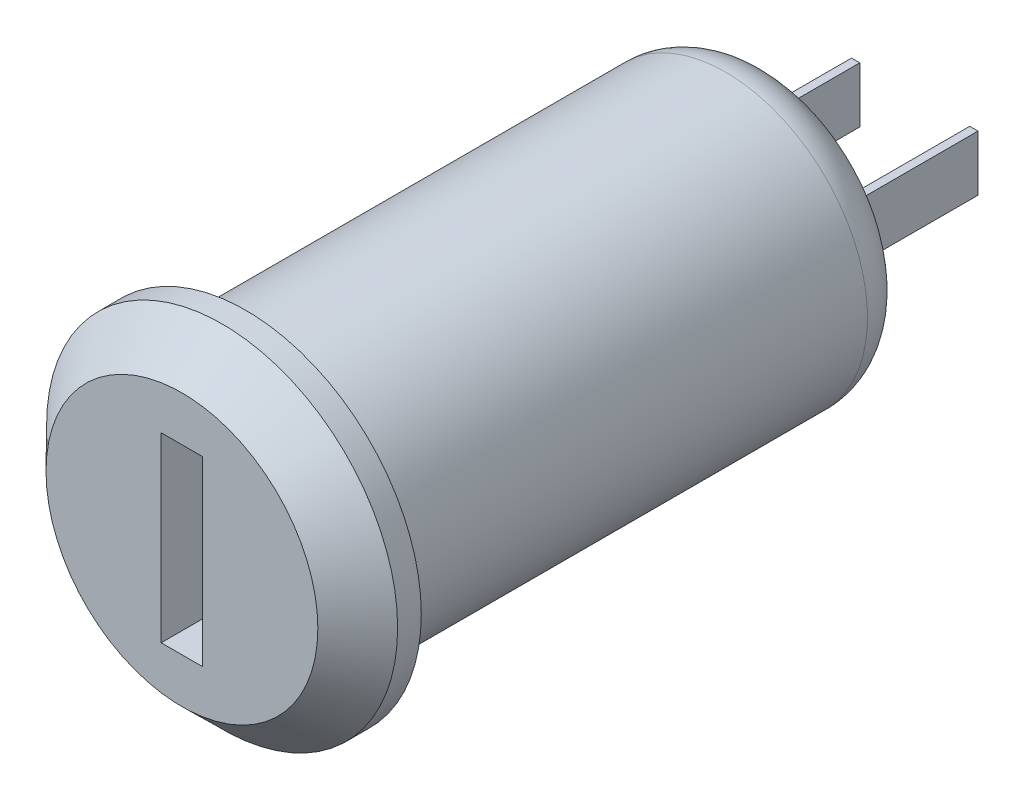
SolidWorks part; units mm, degrees
ref_plane "Front Plane" through (0, 0, 0) normal (0, 0, 1) x (1, 0, 0)
ref_plane "Top Plane" through (0, 0, 0) normal (0, 1, 0) x (1, 0, 0)
ref_plane "Right Plane" through (0, 0, 0) normal (1, 0, 0) x (0, 0, -1)
sketch "Sketch1" plane through (0, 0, 0) normal (0, 1, 0) x (1, 0, 0)
  line L0 (-7.425, -2.2335) -> (-5.75, -3.9335)
  line L2 (0, 0) -> (0, 21.0665)
  line L3 (0, 21.0665) -> (-6, 21.0665)
  line L4 (-6, -1.2335) -> (-6, 21.0665)
  line L5 (-6, -1.2335) -> (-7.425, -1.2335)
  line L6 (0, 0) -> (0, -3.9335)
  line L7 (0, -3.9335) -> (-5.75, -3.9335)
  line L8 (-7.425, -1.2335) -> (-7.425, -2.2335)
  line L9 (0, 16.306) -> (0, -9.832) construction
  dimension "D1" = 12
  dimension "D2" = 14.85
  dimension "D3" = 11.5
  dimension "D4" = 2.7
  dimension "D5" = 25
  dimension "D6" = 1
revolve "Revolve1" add sketch "Sketch1" angle 360 about L9
sketch "Sketch2" plane through (0, 0, 3.9335) normal (0, 0, 1) x (1, 0, 0)
  line L1 (0.8773, -3.8466) -> (-0.8773, -3.8466)
  line L2 (0.8773, -3.8466) -> (0.8773, 3.8466)
  line L3 (0.8773, 3.8466) -> (-0.8773, 3.8466)
  line L4 (-0.8773, -3.8466) -> (-0.8773, 3.8466)
  line L5 (0.8773, -3.8466) -> (-0.8773, 3.8466) construction
  line L6 (0.8773, 3.8466) -> (-0.8773, -3.8466) construction
  point P0 (0, 0)
extrude "Cut-Extrude1" cut sketch "Sketch2" against normal blind 10
sketch "Sketch3" plane through (0, 0, -21.0665) normal (0, 0, -1) x (-1, 0, 0)
  line L0 (-2.5, 0) -> (2.5, 0) construction
  line L1 (-2.325, 1.175) -> (-2.675, 1.175)
  line L2 (-2.325, 1.175) -> (-2.325, -1.175)
  line L3 (-2.325, -1.175) -> (-2.675, -1.175)
  line L4 (-2.675, 1.175) -> (-2.675, -1.175)
  line L5 (-2.325, 1.175) -> (-2.675, -1.175) construction
  line L6 (-2.325, -1.175) -> (-2.675, 1.175) construction
  line L7 (2.675, 1.175) -> (2.325, 1.175)
  line L8 (2.675, 1.175) -> (2.675, -1.175)
  line L9 (2.675, -1.175) -> (2.325, -1.175)
  line L10 (2.325, 1.175) -> (2.325, -1.175)
  line L11 (2.675, 1.175) -> (2.325, -1.175) construction
  line L12 (2.675, -1.175) -> (2.325, 1.175) construction
  point P0 (-2.5, 0)
  point P5 (2.5, 0)
  dimension "D1" = 5
  dimension "D2" = 0.35
  dimension "D3" = 2.35
extrude "Boss-Extrude1" add sketch "Sketch3" along normal blind 6
fillet "Fillet1" radius 2 1 edges at (-6, 0, -21.0665)
